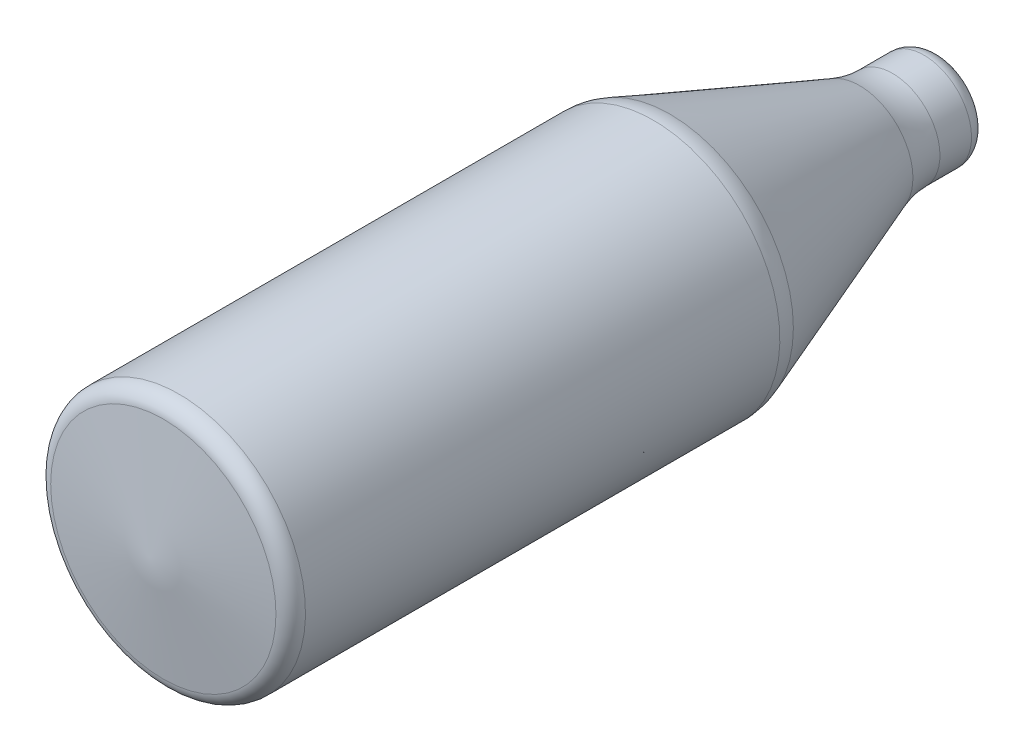
SolidWorks part; units mm, degrees
ref_plane "Front" through (0, 0, 0) normal (0, 0, 1) x (1, 0, 0)
ref_plane "Top" through (0, 0, 0) normal (0, 1, 0) x (1, 0, 0)
ref_plane "Right" through (0, 0, 0) normal (1, 0, 0) x (0, 0, -1)
sketch "Sketch1" plane through (0, 0, 0) normal (1, 0, 0) x (0, 0, -1)
  line L0 (-179.9761, 0) -> (320.0239, 0) construction
  line L1 (-179.9761, 0) -> (-171.0929, 71.2374)
  line L2 (-161.1697, 80) -> (138.8303, 80)
  line L3 (149.2418, 78.1354) -> (269.2418, 33.7292)
  line L4 (290.0649, 30) -> (310.0239, 30)
  line L5 (320.0239, 20) -> (320.0239, 0)
  line L6 (-170.0529, -1.2374) -> (-161.1697, 70)
  line L7 (-161.1697, 70) -> (138.8303, 70)
  line L8 (145.7713, 68.7569) -> (265.7713, 24.3508)
  line L9 (290.0649, 20) -> (310.0239, 20)
  line L10 (310.0239, 20) -> (310.0239, 0)
  arc A0 (-171.0929, 71.2374) -> (-161.1697, 80) centre (-161.1697, 70) cw
  arc A1 (149.2418, 78.1354) -> (138.8303, 80) centre (138.8303, 50) ccw
  arc A2 (269.2418, 33.7292) -> (290.0649, 30) centre (290.0649, 90) ccw
  arc A3 (320.0239, 20) -> (310.0239, 30) centre (310.0239, 20) ccw
  arc A4 (-161.1697, 70) -> (-161.1697, 70) centre (-161.1697, 70) cw
  arc A5 (145.7713, 68.7569) -> (138.8303, 70) centre (138.8303, 50) ccw
  arc A6 (265.7713, 24.3508) -> (290.0649, 20) centre (290.0649, 90) ccw
  arc A7 (310.0239, 20) -> (310.0239, 20) centre (310.0239, 20) ccw
  point P29 (320.0239, 10)
  dimension "D2" = 10
  dimension "D3" = 30
  dimension "D4" = 60
  dimension "D5" = 10
  dimension "D1" = 500
  dimension "D6" = 300
  dimension "D7" = 120
  dimension "D9" = 80
  dimension "D10" = 10
  dimension "D8" = 10
revolve "Revolve2" add sketch "Sketch1" angle 360 about L0
